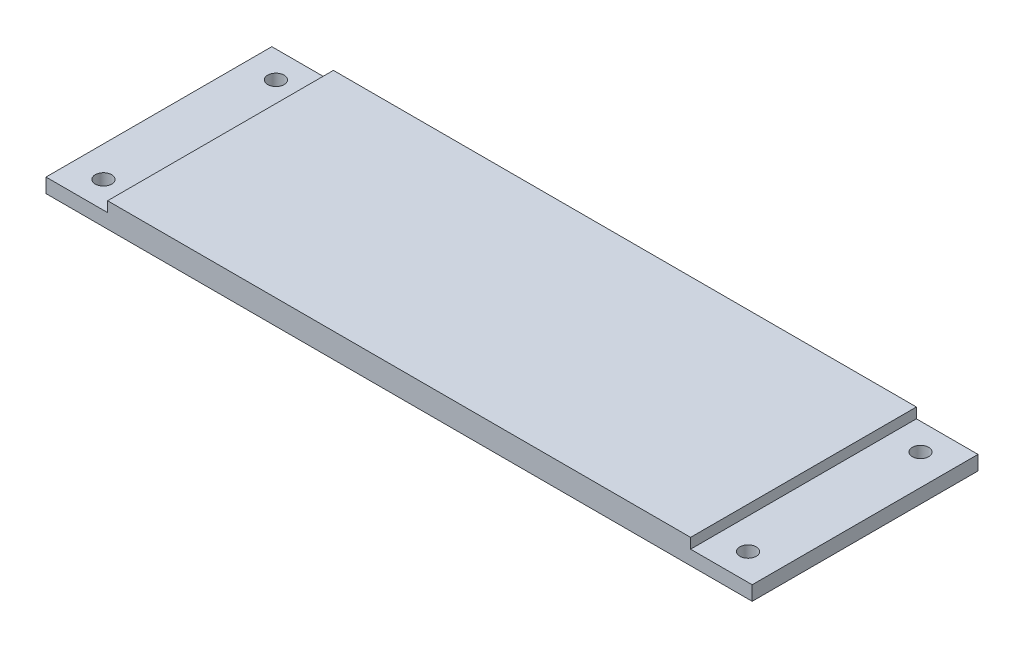
SolidWorks part; units mm, degrees
ref_plane "Plan de face" through (0, 0, 0) normal (0, 0, 1) x (1, 0, 0)
ref_plane "Plan de dessus" through (0, 0, 0) normal (0, 1, 0) x (1, 0, 0)
ref_plane "Plan de droite" through (0, 0, 0) normal (1, 0, 0) x (0, 0, -1)
sketch "Esquisse1" plane through (0, 0, 0) normal (0, 1, 0) x (1, 0, 0)
  line L1 (-86, 27.5) -> (86, 27.5)
  line L2 (-86, 27.5) -> (-86, -27.5)
  line L3 (-86, -27.5) -> (86, -27.5)
  line L4 (86, 27.5) -> (86, -27.5)
  dimension "D1" = 55
  dimension "D2" = 172
  dimension "D3" = 86
  dimension "D4" = 27.5
extrude "Boss.-Extru.1" add sketch "Esquisse1" along normal blind 3.5
sketch "Esquisse2" plane through (0, 3.5, 0) normal (0, 1, 0) x (1, 0, 0)
  line L0 (0, 47.2168) -> (0, -49.3691) construction
  line L1 (-78.5, 23.5287) -> (-78.5, -43.7317) construction
  line L2 (-86, -27.5) -> (86, -27.5) construction
  line L3 (-86, 27.5) -> (-86, -27.5) construction
  line L4 (78.5, 23.5287) -> (78.5, -43.7317) construction
  circle A0 centre (-78.5, 21) radius 2
  circle A1 centre (-78.5, -21) radius 2
  circle A2 centre (78.5, -21) radius 2
  circle A3 centre (78.5, 21) radius 2
  dimension "D1" = 4
  dimension "D2" = 4
  dimension "D4" = 6.5
  dimension "D3" = 42
  dimension "D5" = 7.5
extrude "Enlèv. mat.-Extru.1" cut sketch "Esquisse2" against normal blind 6
sketch "Esquisse3" plane through (0, 3.5, 0) normal (0, 1, 0) x (1, 0, 0)
  line L0 (86, 27.5) -> (-86, 27.5) construction
  line L1 (-71, 27.5) -> (71, 27.5)
  line L2 (-71, 27.5) -> (-71, -27.5)
  line L3 (-71, -27.5) -> (71, -27.5)
  line L4 (71, 27.5) -> (71, -27.5)
  line L5 (-86, -27.5) -> (86, -27.5) construction
  line L6 (-86, 27.5) -> (-86, -27.5) construction
  dimension "D1" = 142
  dimension "D2" = 55
  dimension "D3" = 15
extrude "Boss.-Extru.2" add sketch "Esquisse3" along normal blind 2.5
equation "\"D3@Esquisse1\"=\"D2@Esquisse1\"/2"
equation "\"D4@Esquisse1\"=\"D1@Esquisse1\"/2"
